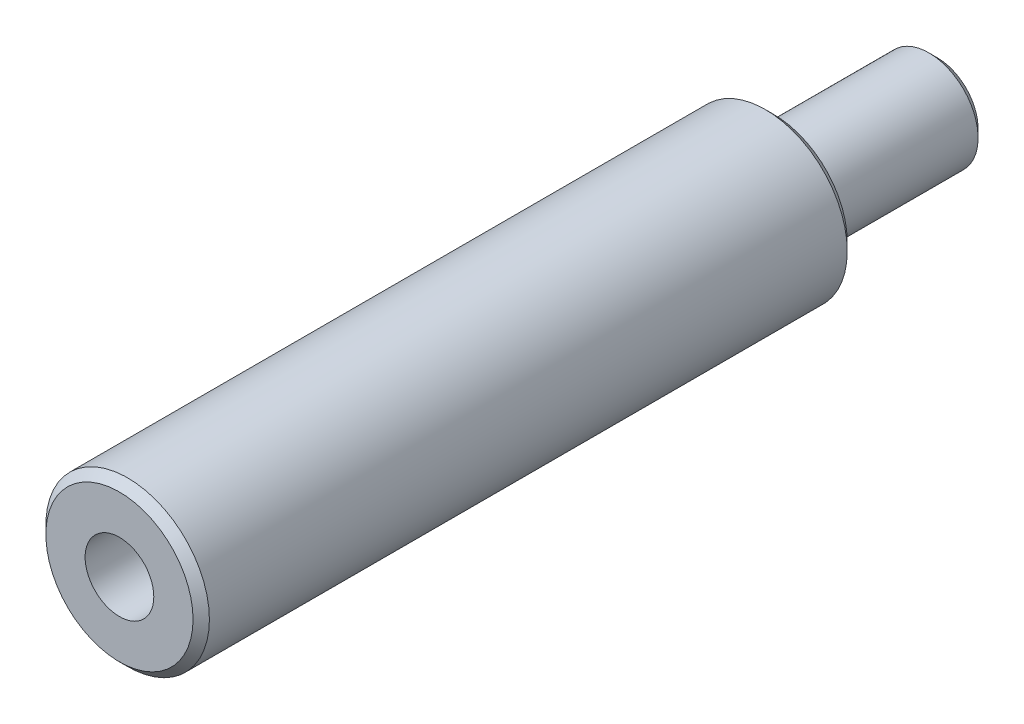
SolidWorks part; units mm, degrees
material "Alumine"
ref_plane "Plan de face" through (0, 0, 0) normal (0, 0, 1) x (1, 0, 0)
ref_plane "Plan de dessus" through (0, 0, 0) normal (0, 1, 0) x (1, 0, 0)
ref_plane "Plan de droite" through (0, 0, 0) normal (1, 0, 0) x (0, 0, -1)
sketch "Esquisse1" plane through (0, 0, 0) normal (0, 0, 1) x (1, 0, 0)
  circle A0 centre (0, 0) radius 5
  dimension "D1" = 10
extrude "Boss.-Extru.1" add sketch "Esquisse1" along normal blind 40
sketch "Esquisse2" plane through (0, 0, 0) normal (0, 0, -1) x (-1, 0, 0)
  circle A0 centre (0, 0) radius 3
  dimension "D1" = 6
extrude "Boss.-Extru.2" add sketch "Esquisse2" along normal blind 10
hole_wizard "Trou pour taraudage pour trou taraudé M51" positions "Esquisse3" profile "Esquisse4" hole size "M5" standard "ISO"
sketch "Esquisse3" plane through (0, 0, 40) normal (0, 0, 1) x (1, 0, 0)
  point P0 (0, 0)
sketch "Esquisse4" plane through (0, 0, 40) normal (1, 0, 0) x (0, -1, 0)
  line L0 (0, 0) -> (0, 11.2618)
  line L1 (0, 11.2618) -> (2.1, 10)
  line L2 (2.1, 10) -> (2.1, 0)
  line L5 (2.1, 0) -> (0, 0)
  line L10 (0, 11.2618) -> (-2.1, 10) construction
  line L11 (0, -6.35) -> (0, 107.95) construction
  dimension "Diamètre du perçage" = 4.2
  dimension "Profondeur du perçage" = 10
  dimension "Angle de pointe" = 118
chamfer "Chanfrein1" distance 0.5 angle 45 3 edges at (5, 0, 0) (5, 0, 40) (-3, 0, -10)
